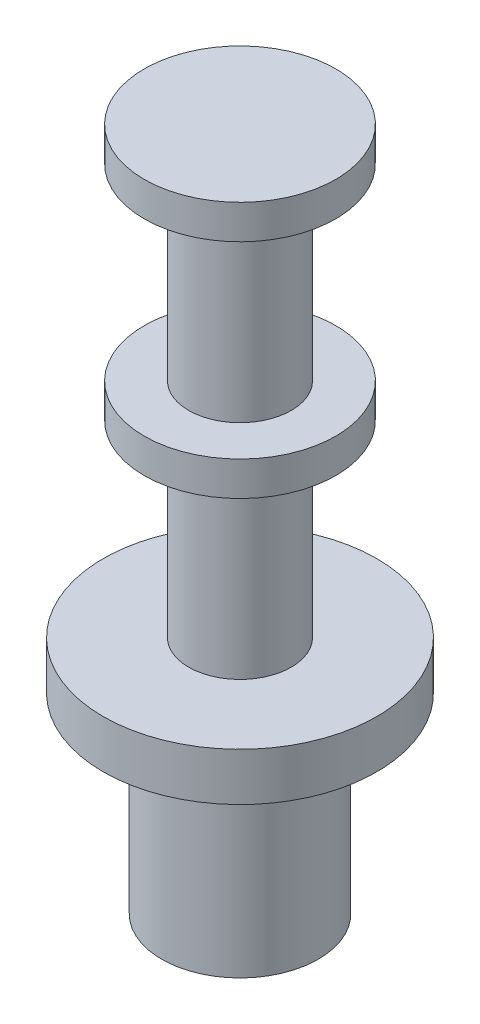
SolidWorks part; units mm, degrees
material "Brass"
ref_plane "Front Plane" through (0, 0, 0) normal (0, 0, 1) x (1, 0, 0)
ref_plane "Top Plane" through (0, 0, 0) normal (0, 1, 0) x (1, 0, 0)
ref_plane "Right Plane" through (0, 0, 0) normal (1, 0, 0) x (0, 0, -1)
sketch "Sketch1" plane through (0, 0, 0) normal (0, 1, 0) x (1, 0, 0)
  circle A0 centre (0, 0) radius 2
  dimension "D1" = 4
extrude "Boss-Extrude1" add sketch "Sketch1" along normal blind 0.7
sketch "Sketch2" plane through (0, 0.7, 0) normal (0, 1, 0) x (1, 0, 0)
  circle A0 centre (0, 0) radius 0.75
  dimension "D1" = 1.5
extrude "Boss-Extrude2" add sketch "Sketch2" along normal blind 2.75
sketch "Sketch3" plane through (0, 3.45, 0) normal (0, 1, 0) x (1, 0, 0)
  circle A0 centre (0, 0) radius 1.4
  dimension "D1" = 2.8
extrude "Boss-Extrude3" add sketch "Sketch3" along normal blind 0.5
sketch "Sketch4" plane through (0, 3.95, 0) normal (0, 1, 0) x (1, 0, 0)
  circle A0 centre (0, 0) radius 0.75
  dimension "D1" = 1.5
extrude "Boss-Extrude4" add sketch "Sketch4" along normal blind 2.75
sketch "Sketch5" plane through (0, 6.7, 0) normal (0, 1, 0) x (1, 0, 0)
  circle A0 centre (0, 0) radius 1.4
  dimension "D1" = 2.8
extrude "Boss-Extrude5" add sketch "Sketch5" along normal blind 0.5
sketch "Sketch6" plane through (0, 0, 0) normal (0, -1, 0) x (1, 0, 0)
  circle A0 centre (0, 0) radius 1.145
  dimension "D1" = 2.29
extrude "Boss-Extrude6" add sketch "Sketch6" along normal blind 2.8
